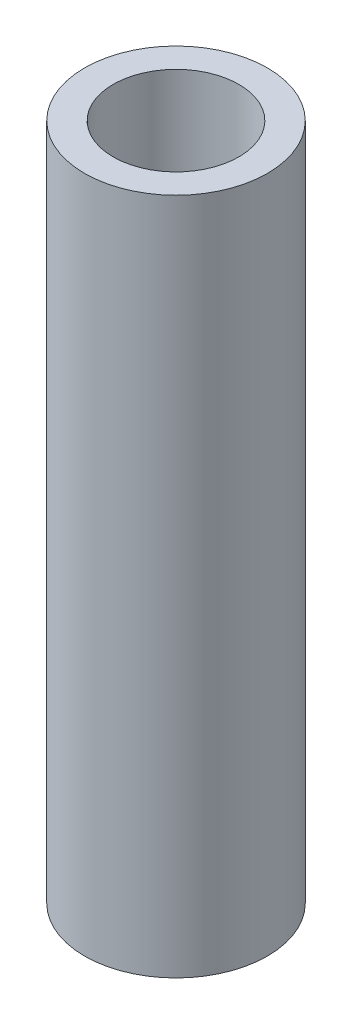
SolidWorks part; units mm, degrees
ref_plane "Front Plane" through (0, 0, 0) normal (0, 0, 1) x (1, 0, 0)
ref_plane "Top Plane" through (0, 0, 0) normal (0, 1, 0) x (1, 0, 0)
ref_plane "Right Plane" through (0, 0, 0) normal (1, 0, 0) x (0, 0, -1)
sketch "Sketch1" plane through (0, 0, 0) normal (0, 1, 0) x (1, 0, 0)
  circle A0 centre (0, 0) radius 7.4168
  dimension "D1" = 14.8336
extrude "Boss-Extrude1" add sketch "Sketch1" along normal blind 55
hole_wizard "M12x1.75 Tapped Hole1" positions "Sketch2" profile "Sketch3" tap size "M12x1.75" standard "ANSI Metric" end condition through all
sketch "Sketch2" plane through (0, 55, 0) normal (0, 1, 0) x (1, 0, 0)
  point P0 (0, 0)
sketch "Sketch3" plane through (0, 55, 0) normal (1, 0, 0) x (0, 0, 1)
  line L0 (0, 0) -> (0, 55)
  line L1 (0, 55) -> (5.1, 55)
  line L2 (5.1, 55) -> (5.1, 0)
  line L5 (5.1, 0) -> (0, 0)
  line L11 (0, -6.35) -> (0, 107.95) construction
  dimension "Thru Tap Drill Dia." = 10.2
  dimension "Thru Tap Drill Depth" = 55
cosmetic thread "Hole Thread1" parameters "D2"=12
equation "\"diameter\"= 14.833600mm"
equation "\"length\"= 55mm"
equation "\"D1@Boss-Extrude1\"=\"length\""
